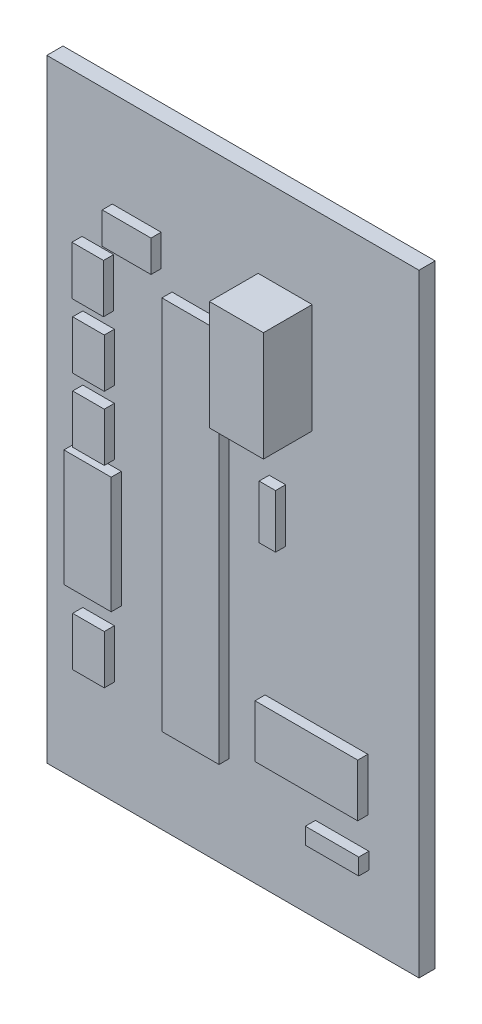
SolidWorks part; units mm, degrees
ref_plane "Front Plane" through (0, 0, 0) normal (0, 0, 1) x (1, 0, 0)
ref_plane "Top Plane" through (0, 0, 0) normal (0, 1, 0) x (1, 0, 0)
ref_plane "Right Plane" through (0, 0, 0) normal (1, 0, 0) x (0, 0, -1)
sketch "Sketch1" plane through (0, 0, 0) normal (0, 0, 1) x (1, 0, 0)
  line L0 (0, 0) -> (36.81, 0)
  line L1 (36.81, 0) -> (36.81, 60.63)
  line L2 (36.81, 60.63) -> (0, 60.63)
  line L3 (0, 60.63) -> (0, 0)
extrude "BOARD" add sketch "Sketch1" along normal blind 1.6 separate body
ref_plane "Plane1" through (0, 0, 1.6) normal (0, 0, 1) x (1, 0, 0)
sketch "Sketch2" plane through (0, 0, 1.6) normal (0, 0, 1) x (1, 0, 0)
  line L0 (6.477, 51.1302) -> (11.303, 51.1302)
  line L1 (11.303, 51.1302) -> (11.303, 48.006)
  line L2 (11.303, 48.006) -> (6.477, 48.006)
  line L3 (6.477, 48.006) -> (6.477, 51.1302)
extrude "C025-030X050-1" add sketch "Sketch2" along normal blind 1 separate body
sketch "Sketch3" plane through (0, 0, 1.6) normal (0, 0, 1) x (1, 0, 0)
  line L0 (3.4798, 42.037) -> (3.4798, 46.863)
  line L1 (3.4798, 46.863) -> (6.604, 46.863)
  line L2 (6.604, 46.863) -> (6.604, 42.037)
  line L3 (6.604, 42.037) -> (3.4798, 42.037)
extrude "C025-030X050-2" add sketch "Sketch3" along normal blind 1 separate body
sketch "Sketch4" plane through (0, 0, 1.6) normal (0, 0, 1) x (1, 0, 0)
  line L0 (6.6802, 40.513) -> (6.6802, 35.687)
  line L1 (6.6802, 35.687) -> (3.556, 35.687)
  line L2 (3.556, 35.687) -> (3.556, 40.513)
  line L3 (3.556, 40.513) -> (6.6802, 40.513)
extrude "C025-030X050-3" add sketch "Sketch4" along normal blind 1 separate body
sketch "Sketch5" plane through (0, 0, 1.6) normal (0, 0, 1) x (1, 0, 0)
  line L0 (6.6802, 34.163) -> (6.6802, 29.337)
  line L1 (6.6802, 29.337) -> (3.556, 29.337)
  line L2 (3.556, 29.337) -> (3.556, 34.163)
  line L3 (3.556, 34.163) -> (6.6802, 34.163)
extrude "C025-030X050-4" add sketch "Sketch5" along normal blind 1 separate body
sketch "Sketch6" plane through (0, 0, 1.6) normal (0, 0, 1) x (1, 0, 0)
  line L0 (6.6802, 15.113) -> (6.6802, 10.287)
  line L1 (6.6802, 10.287) -> (3.556, 10.287)
  line L2 (3.556, 10.287) -> (3.556, 15.113)
  line L3 (3.556, 15.113) -> (6.6802, 15.113)
extrude "C025-030X050-5" add sketch "Sketch6" along normal blind 1 separate body
sketch "Sketch7" plane through (0, 0, 1.6) normal (0, 0, 1) x (1, 0, 0)
  line L0 (31.75, 16.637) -> (31.75, 11.43)
  line L1 (31.75, 11.43) -> (21.59, 11.43)
  line L2 (21.59, 11.43) -> (21.59, 16.637)
  line L3 (21.59, 16.637) -> (31.75, 16.637)
extrude "AB9V-1" add sketch "Sketch7" along normal blind 1 separate body
sketch "Sketch8" plane through (0, 0, 1.6) normal (0, 0, 1) x (1, 0, 0)
  line L0 (12.3825, 46.5455) -> (18.034, 46.5455)
  line L1 (18.034, 46.5455) -> (18.034, 9.398)
  line L2 (18.034, 9.398) -> (12.3825, 9.398)
  line L3 (12.3825, 9.398) -> (12.3825, 46.5455)
extrude "DIL28-1" add sketch "Sketch8" along normal blind 1 separate body
sketch "Sketch9" plane through (0, 0, 0) normal (0, 0, 1) x (1, 0, 0)
  line L0 (31.7735, 35.5835) -> (26.0711, 35.5835)
  line L1 (26.0711, 35.5835) -> (26.0711, 30.1271)
  line L2 (26.0711, 30.1271) -> (31.7735, 30.1271)
  line L3 (31.7735, 30.1271) -> (31.7735, 35.5835)
extrude "RGBLED5050-1" add sketch "Sketch9" against normal blind 1 separate body
sketch "Sketch10" plane through (0, 0, 1.6) normal (0, 0, 1) x (1, 0, 0)
  line L0 (26.245, 52.405) -> (26.245, 41.575)
  line L1 (26.245, 41.575) -> (20.9, 41.575)
  line L2 (20.9, 41.575) -> (20.9, 52.405)
  line L3 (20.9, 52.405) -> (26.245, 52.405)
extrude "TO254P482X997X1968-3P_4.820000-1" add sketch "Sketch10" along normal blind 4.82 separate body
sketch "Sketch11" plane through (0, 0, 1.6) normal (0, 0, 1) x (1, 0, 0)
  line L0 (21.9964, 30.3784) -> (21.9964, 35.6616)
  line L1 (21.9964, 35.6616) -> (23.622, 35.6616)
  line L2 (23.622, 35.6616) -> (23.622, 30.3784)
  line L3 (23.622, 30.3784) -> (21.9964, 30.3784)
extrude "AXIAL-0_3-1" add sketch "Sketch11" along normal blind 1 separate body
sketch "Sketch12" plane through (0, 0, 1.6) normal (0, 0, 1) x (1, 0, 0)
  line L0 (31.8516, 6.7564) -> (26.5684, 6.7564)
  line L1 (26.5684, 6.7564) -> (26.5684, 8.382)
  line L2 (26.5684, 8.382) -> (31.8516, 8.382)
  line L3 (31.8516, 8.382) -> (31.8516, 6.7564)
extrude "AXIAL-0_3-2" add sketch "Sketch12" along normal blind 1 separate body
sketch "Sketch13" plane through (0, 0, 0) normal (0, 0, 1) x (1, 0, 0)
  line L0 (31.3055, 42.3545) -> (31.3055, 54.102)
  line L1 (31.3055, 54.102) -> (27.178, 54.102)
  line L2 (27.178, 54.102) -> (27.178, 42.3545)
  line L3 (27.178, 42.3545) -> (31.3055, 42.3545)
extrude "EG1218-1" add sketch "Sketch13" against normal blind 1 separate body
sketch "Sketch14" plane through (0, 0, 0) normal (0, 0, 1) x (1, 0, 0)
  line L0 (33.16, 22.22) -> (25.26, 22.22)
  line L1 (25.26, 22.22) -> (25.26, 18.42)
  line L2 (25.26, 18.42) -> (33.16, 18.42)
  line L3 (33.16, 18.42) -> (33.16, 22.22)
extrude "TACT_PANA-EVQ-1" add sketch "Sketch14" against normal blind 1 separate body
sketch "Sketch15" plane through (0, 0, 1.6) normal (0, 0, 1) x (1, 0, 0)
  line L0 (7.366, 28.6766) -> (7.366, 17.145)
  line L1 (7.366, 17.145) -> (2.6924, 17.145)
  line L2 (2.6924, 17.145) -> (2.6924, 28.6766)
  line L3 (2.6924, 28.6766) -> (7.366, 28.6766)
extrude "HC49US-1" add sketch "Sketch15" along normal blind 1 separate body
sketch "Sketch16" plane through (0, 0, -1) normal (0, 0, -1) x (-1, 0, 0)
  line L0 (-31.7735, 32.8553) -> (-26.0711, 32.8553) construction
  line L1 (-31.7735, 30.1271) -> (-31.7735, 35.5835) construction
  line L2 (-26.0711, 35.5835) -> (-26.0711, 30.1271) construction
  line L3 (-28.9223, 30.1271) -> (-28.9223, 35.5835) construction
  line L4 (-26.0711, 30.1271) -> (-31.7735, 30.1271) construction
  line L5 (-31.7735, 35.5835) -> (-26.0711, 35.5835) construction
  line L12 (-29.2417, 54.102) -> (-29.2417, 42.3545) construction
  line L13 (-31.3055, 54.102) -> (-27.178, 54.102) construction
  line L14 (-27.178, 42.3545) -> (-31.3055, 42.3545) construction
  line L15 (-27.178, 54.102) -> (-27.178, 42.3545) construction
  line L16 (-27.178, 48.2283) -> (-31.3055, 48.2283) construction
  line L17 (-31.3055, 42.3545) -> (-31.3055, 54.102) construction
  line L20 (-25.26, 20.32) -> (-33.16, 20.32) construction
  line L21 (-25.26, 22.22) -> (-25.26, 18.42) construction
  line L22 (-33.16, 18.42) -> (-33.16, 22.22) construction
  line L23 (-29.21, 22.22) -> (-29.21, 18.42) construction
  line L24 (-33.16, 22.22) -> (-25.26, 22.22) construction
  line L25 (-25.26, 18.42) -> (-33.16, 18.42) construction
